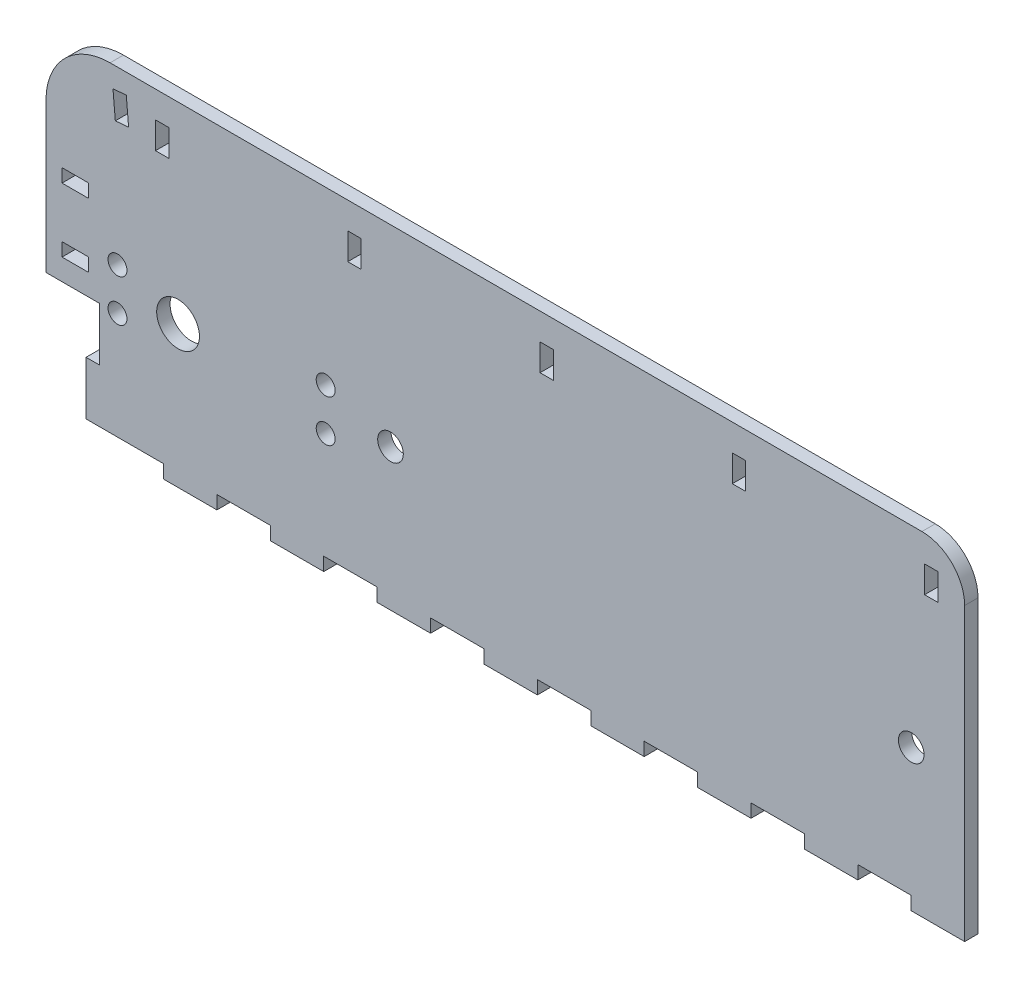
SolidWorks part; units mm, degrees
ref_plane "Front" through (0, 0, 0) normal (0, 0, 1) x (1, 0, 0)
ref_plane "Top" through (0, 0, 0) normal (0, 1, 0) x (1, 0, 0)
ref_plane "Right" through (0, 0, 0) normal (1, 0, 0) x (0, 0, -1)
sketch "Sketch1" plane through (0, 0, 0) normal (0, 0, 1) x (1, 0, 0)
  line L5 (0, 0) -> (228.6, 0)
  line L6 (0, 0) -> (0, 76.2)
  line L7 (0, 76.2) -> (228.6, 76.2)
  line L8 (228.6, 0) -> (228.6, 76.2)
  circle A0 centre (215.9, 30.48) radius 3.048
  circle A1 centre (92.075, 30.48) radius 3.048
  circle A2 centre (41.5608, 30.48) radius 5.08
  dimension "D7" = 6.096
  dimension "D8" = 6.096
  dimension "D9" = 10.16
  dimension "D1" = 228.6
  dimension "D2" = 76.2
  dimension "D3" = 50.5142
  dimension "D4" = 123.825
  dimension "D5" = 30.48
  dimension "D6" = 12.7
extrude "Boss-Extrude1" add sketch "Sketch1" along normal blind 3.175
sketch "Sketch2" plane through (0, 0, 0) normal (0, -1, 0) x (1, 0, 0)
  line L0 (0, 3.175) -> (228.6, 3.175) construction
  line L1 (228.6, 0) -> (215.9, 0)
  line L2 (228.6, 0) -> (228.6, 3.175)
  line L3 (228.6, 3.175) -> (215.9, 3.175)
  line L4 (215.9, 0) -> (215.9, 3.175)
  line L5 (203.2, 0) -> (203.2, 3.175)
  line L6 (203.2, 0) -> (190.5, 0)
  line L7 (190.5, 0) -> (190.5, 3.175)
  line L8 (203.2, 3.175) -> (190.5, 3.175)
  line L9 (177.8, 0) -> (177.8, 3.175)
  line L10 (177.8, 0) -> (165.1, 0)
  line L11 (165.1, 0) -> (165.1, 3.175)
  line L12 (177.8, 3.175) -> (165.1, 3.175)
  line L13 (152.4, 0) -> (152.4, 3.175)
  line L14 (152.4, 0) -> (139.7, 0)
  line L15 (139.7, 0) -> (139.7, 3.175)
  line L16 (152.4, 3.175) -> (139.7, 3.175)
  line L17 (127, 0) -> (127, 3.175)
  line L18 (127, 0) -> (114.3, 0)
  line L19 (114.3, 0) -> (114.3, 3.175)
  line L20 (127, 3.175) -> (114.3, 3.175)
  line L21 (101.6, 0) -> (101.6, 3.175)
  line L22 (101.6, 0) -> (88.9, 0)
  line L23 (88.9, 0) -> (88.9, 3.175)
  line L24 (101.6, 3.175) -> (88.9, 3.175)
  line L25 (76.2, 0) -> (76.2, 3.175)
  line L26 (76.2, 0) -> (63.5, 0)
  line L27 (63.5, 0) -> (63.5, 3.175)
  line L28 (76.2, 3.175) -> (63.5, 3.175)
  line L29 (50.8, 0) -> (50.8, 3.175)
  line L30 (50.8, 0) -> (38.1, 0)
  line L31 (38.1, 0) -> (38.1, 3.175)
  line L32 (50.8, 3.175) -> (38.1, 3.175)
  dimension "D1" = 12.7
  dimension "D2" = 8
extrude "Boss-Extrude2" add sketch "Sketch2" along normal blind 3.175
sketch "Sketch3" plane through (0, 0, 0) normal (0, 0, -1) x (-1, 0, 0)
  line L1 (0, 0) -> (-22.86, 0)
  line L2 (0, 0) -> (0, 25.4)
  line L3 (0, 25.4) -> (-22.86, 25.4)
  line L4 (-22.86, 0) -> (-22.86, 25.4)
  dimension "D1" = 25.4
  dimension "D2" = 22.86
extrude "Cut-Extrude1" cut sketch "Sketch3" against normal through all
sketch "Sketch4" plane through (22.86, 0, 0) normal (-1, 0, 0) x (0, 0, 1)
  line L0 (3.175, 25.4) -> (3.175, 0) construction
  line L1 (0, 0) -> (3.175, 0)
  line L2 (0, 0) -> (0, 12.7)
  line L3 (0, 12.7) -> (3.175, 12.7)
  line L4 (3.175, 0) -> (3.175, 12.7)
  dimension "D1" = 12.7
extrude "Boss-Extrude3" add sketch "Sketch4" along normal blind 3.175
sketch "Sketch6" plane through (0, 0, 0) normal (0, 0, -1) x (-1, 0, 0)
  circle A0 centre (-27.1608, 35.48) radius 2.25
  circle A1 centre (-27.1608, 25.48) radius 2.25
  circle A2 centre (-76.6608, 35.48) radius 2.25
  circle A3 centre (-76.6608, 25.48) radius 2.25
extrude "Cut-Extrude2" cut sketch "Sketch6" against normal through all
sketch "Sketch8" plane through (0, 0, 3.175) normal (0, 0, 1) x (1, 0, 0)
  line L8 (0, 76.2) -> (10.16, 76.2)
  line L9 (0, 76.2) -> (0, 25.4)
  line L10 (0, 25.4) -> (10.16, 25.4)
  line L11 (10.16, 76.2) -> (10.16, 25.4)
  line L12 (0, 25.4) -> (22.86, 25.4) construction
  line L13 (22.86, 25.4) -> (22.86, 12.7) construction
  dimension "D1" = 12.7
extrude "Cut-Extrude3" cut sketch "Sketch8" against normal through all
sketch "Sketch12" plane through (0, 0, 0) normal (0, 0, -1) x (-1, 0, 0)
  line L0 (-164.0363, 64) -> (-164.0363, 1) construction
  line L1 (-139.0363, 1) -> (-139.0363, 64) construction
  line L2 (-140.0363, 65) -> (-163.0363, 65) construction
  line L3 (-164.0363, 64) -> (-164.0363, 1) construction
  line L4 (-139.0363, 1) -> (-139.0363, 64) construction
  line L5 (-140.0363, 65) -> (-163.0363, 65) construction
  line L6 (-228.6, 76.2) -> (-10.16, 76.2) construction
  line L7 (-222.25, 69.85) -> (-219.075, 69.85)
  line L8 (-222.25, 69.85) -> (-222.25, 63.5)
  line L9 (-222.25, 63.5) -> (-219.075, 63.5)
  line L10 (-219.075, 69.85) -> (-219.075, 63.5)
  line L11 (-228.6, -3.175) -> (-228.6, 76.2) construction
  line L12 (-176.53, 69.85) -> (-176.53, 63.5)
  line L13 (-176.53, 69.85) -> (-173.355, 69.85)
  line L14 (-173.355, 69.85) -> (-173.355, 63.5)
  line L15 (-176.53, 63.5) -> (-173.355, 63.5)
  line L16 (-130.81, 69.85) -> (-130.81, 63.5)
  line L17 (-130.81, 69.85) -> (-127.635, 69.85)
  line L18 (-127.635, 69.85) -> (-127.635, 63.5)
  line L19 (-130.81, 63.5) -> (-127.635, 63.5)
  line L20 (-85.09, 69.85) -> (-85.09, 63.5)
  line L21 (-85.09, 69.85) -> (-81.915, 69.85)
  line L22 (-81.915, 69.85) -> (-81.915, 63.5)
  line L23 (-85.09, 63.5) -> (-81.915, 63.5)
  line L24 (-39.37, 69.85) -> (-39.37, 63.5)
  line L25 (-39.37, 69.85) -> (-36.195, 69.85)
  line L26 (-36.195, 69.85) -> (-36.195, 63.5)
  line L27 (-39.37, 63.5) -> (-36.195, 63.5)
  dimension "D1" = 6.35
  dimension "D2" = 3.175
  dimension "D3" = 6.35
  dimension "D4" = 6.35
  dimension "D5" = 5
extrude "Cut-Extrude5" cut sketch "Sketch12" against normal blind 3.175
sketch "Sketch13" plane through (0, 0, 3.175) normal (0, 0, 1) x (1, 0, 0)
  line L4 (25.4, 60.96) -> (9.8038, 76.5562) construction
  line L9 (10.16, 60.96) -> (10.16, 76.2)
  line L10 (10.16, 76.2) -> (25.4, 76.2)
  arc A0 (10.16, 60.96) -> (25.4, 76.2) centre (25.4, 60.96) cw
  point P10 (10.16, 76.2)
  dimension "D1" = 15.24
extrude "Cut-Extrude6" cut sketch "Sketch13" against normal through all
sketch "Sketch14" plane through (0, 0, 3.175) normal (0, 0, 1) x (1, 0, 0)
  line L0 (20.32, 25.4) -> (20.32, 75.3284) construction
  line L1 (10.16, 25.4) -> (22.86, 25.4) construction
  line L2 (20.32, 30.48) -> (13.97, 30.48)
  line L3 (20.32, 30.48) -> (20.32, 33.655)
  line L4 (20.32, 33.655) -> (13.97, 33.655)
  line L5 (13.97, 30.48) -> (13.97, 33.655)
  line L10 (20.32, 45.72) -> (20.32, 48.895)
  line L11 (20.32, 45.72) -> (13.97, 45.72)
  line L12 (13.97, 45.72) -> (13.97, 48.895)
  line L13 (20.32, 48.895) -> (13.97, 48.895)
  line L14 (22.86, 25.4) -> (22.86, 12.7) construction
  arc A0 (25.4, 76.2) -> (10.16, 60.96) centre (25.4, 60.96) ccw construction
  dimension "D1" = 3.175
  dimension "D2" = 5.08
  dimension "D3" = 6.35
  dimension "D5" = 2.54
  dimension "D4" = 2
extrude "Cut-Extrude7" cut sketch "Sketch14" against normal through all
sketch "Sketch15" plane through (0, 0, 3.175) normal (0, 0, 1) x (1, 0, 0)
  line L0 (10.16, 60.96) -> (228.6, 60.96) construction
  line L1 (228.6, -3.175) -> (228.6, 76.2) construction
  line L2 (28.575, 60.96) -> (25.9804, 90.6169) construction
  line L3 (36.195, 63.5) -> (36.195, 69.85) construction
  line L8 (26.6393, 64.8702) -> (26.0859, 71.196)
  line L9 (26.0859, 71.196) -> (29.2488, 71.4727)
  line L10 (29.2488, 71.4727) -> (29.8023, 65.1469)
  line L11 (29.8023, 65.1469) -> (26.6393, 64.8702)
  point P10 (28.7465, 60.96)
  dimension "D1" = 7.62
  dimension "D2" = 85
  dimension "D3" = 3.175
  dimension "D4" = 6.35
  dimension "D5" = 1.5875
  dimension "D6" = 4.064
extrude "Cut-Extrude8" cut sketch "Sketch15" against normal through all
sketch "Sketch16" plane through (0, 0, 3.175) normal (0, 0, 1) x (1, 0, 0)
  line L4 (218.44, 76.2) -> (228.6, 76.2)
  line L5 (228.6, 76.2) -> (228.6, 66.04)
  arc A0 (228.6, 66.04) -> (218.44, 76.2) centre (218.44, 66.04) ccw
  point P10 (228.6, 76.2)
  dimension "D1" = 10.16
extrude "Cut-Extrude9" cut sketch "Sketch16" against normal through all
